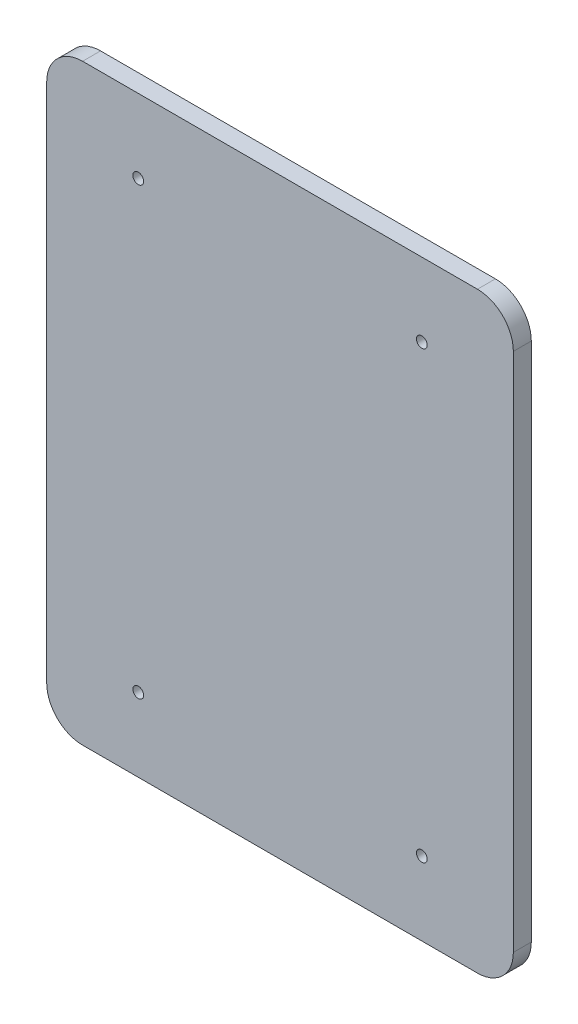
SolidWorks part; units mm, degrees
material "Acrílico (médio-alto impacto)"
ref_plane "Plano frontal" through (0, 0, 0) normal (0, 0, 1) x (1, 0, 0)
ref_plane "Plano superior" through (0, 0, 0) normal (0, 1, 0) x (1, 0, 0)
ref_plane "Plano direito" through (0, 0, 0) normal (1, 0, 0) x (0, 0, -1)
sketch "Esboço1" plane through (0, 0, 0) normal (0, 0, 1) x (1, 0, 0)
  line L1 (-49.2171, -36.3939) -> (60.7829, -36.3939)
  line L2 (-59.2171, -26.3939) -> (-59.2171, 118.6061)
  line L3 (-49.2171, 128.6061) -> (60.7829, 128.6061)
  line L4 (70.7829, -26.3939) -> (70.7829, 118.6061)
  arc A0 (-59.2171, 118.6061) -> (-49.2171, 128.6061) centre (-49.2171, 118.6061) cw
  arc A1 (60.7829, 128.6061) -> (70.7829, 118.6061) centre (60.7829, 118.6061) cw
  arc A2 (60.7829, -36.3939) -> (70.7829, -26.3939) centre (60.7829, -26.3939) ccw
  arc A3 (-49.2171, -36.3939) -> (-59.2171, -26.3939) centre (-49.2171, -26.3939) cw
  point P4 (0, 0)
  dimension "D1" = 10
extrude "Ressalto-extrusão1" add sketch "Esboço1" along normal blind 5
sketch "Esboço2" plane through (0, 0, 0) normal (0, 0, -1) x (-1, 0, 0)
  line L1 (-70.7829, -26.3939) -> (-70.7829, 118.6061) construction
  line L2 (59.2171, 118.6061) -> (59.2171, -26.3939) construction
  line L4 (-60.7829, 128.6061) -> (49.2171, 128.6061) construction
  circle A0 centre (33.7171, -15.8939) radius 1.5
  circle A1 centre (33.7171, 108.1061) radius 1.5
  circle A2 centre (-45.2829, -15.8939) radius 1.5
  circle A3 centre (-45.2829, 108.1061) radius 1.5
  dimension "D1" = 79
  dimension "D2" = 124
  dimension "D3" = 124
  dimension "D4" = 79
  dimension "D5" = 3
  dimension "D6" = 3
  dimension "D7" = 3
  dimension "D8" = 3
  dimension "D9" = 25.5
  dimension "D10" = 25.5
  dimension "D11" = 25.5
  dimension "D12" = 25.5
  dimension "D13" = 20.5
extrude "Corte-extrusão1" cut sketch "Esboço2" against normal blind 5
